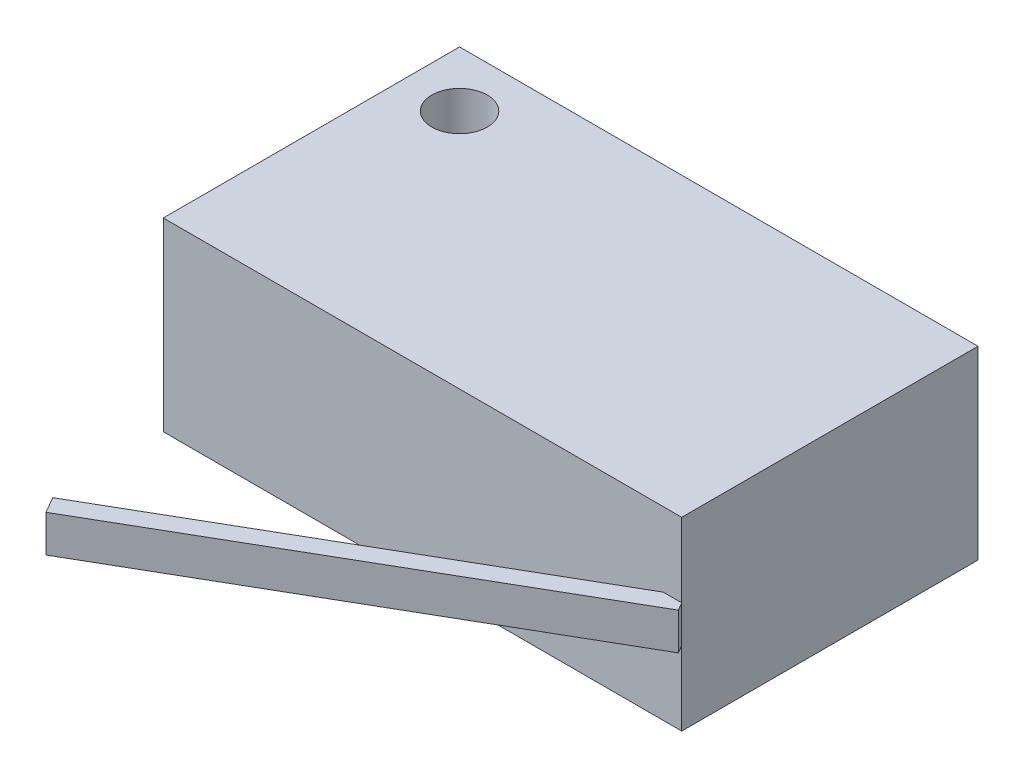
SolidWorks part; units mm, degrees
ref_plane "Front Plane" through (0, 0, 0) normal (0, 0, 1) x (1, 0, 0)
ref_plane "Top Plane" through (0, 0, 0) normal (0, 1, 0) x (1, 0, 0)
ref_plane "Right Plane" through (0, 0, 0) normal (1, 0, 0) x (0, 0, -1)
sketch "Sketch1" plane through (0, 0, 0) normal (0, 1, 0) x (1, 0, 0)
  line L1 (14, -8) -> (-14, -8)
  line L2 (14, -8) -> (14, 8)
  line L3 (14, 8) -> (-14, 8)
  line L4 (-14, -8) -> (-14, 8)
  line L5 (14, -8) -> (-14, 8) construction
  line L6 (14, 8) -> (-14, -8) construction
  point P0 (0, 0)
  dimension "D1" = 16
  dimension "D2" = 28
extrude "Boss-Extrude1" add sketch "Sketch1" along normal blind 10
ref_plane "Plane1" through (6.9641, 0, 12.0622) normal (0.5, 0, 0.866) x (0, -1, 0)
sketch "Sketch2" plane through (6.9641, 0, 12.0622) normal (0.5, 0, 0.866) x (0, -1, 0)
  line L0 (-10, 8.1244) -> (0, 8.1244) construction
  line L1 (-6, -16.8756) -> (-4, -16.8756)
  line L2 (-6, -16.8756) -> (-6, 8.1244)
  line L3 (-6, 8.1244) -> (-4, 8.1244)
  line L4 (-4, -16.8756) -> (-4, 8.1244)
  point P6 (-5, 8.1244)
  point P7 (-5, 8.1244)
  dimension "D1" = 25
  dimension "D2" = 2
extrude "Boss-Extrude2" add sketch "Sketch2" along normal mid plane 1
sketch "Sketch3" plane through (0, 10, 0) normal (0, 1, 0) x (1, 0, 0)
  line L0 (-14, 8) -> (-14, -8) construction
  line L2 (14, 8) -> (-14, 8) construction
  circle A0 centre (-11, 5) radius 1.5
  dimension "D1" = 3
  dimension "D2" = 3
  dimension "D3" = 3
extrude "Cut-Extrude1" cut sketch "Sketch3" against normal up to surface (10 mm away) up to face at (0, 0, 0)
